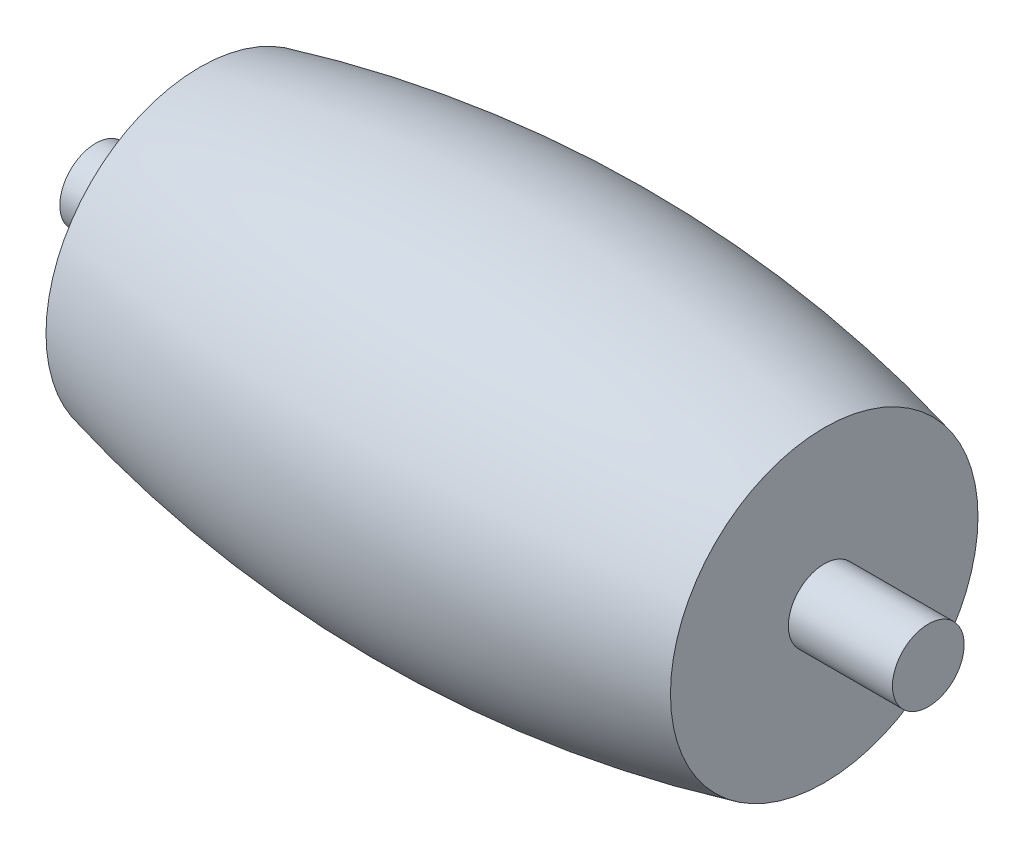
SolidWorks part; units mm, degrees
ref_plane "Front Plane" through (0, 0, 0) normal (0, 0, 1) x (1, 0, 0)
ref_plane "Top Plane" through (0, 0, 0) normal (0, 1, 0) x (1, 0, 0)
ref_plane "Right Plane" through (0, 0, 0) normal (1, 0, 0) x (0, 0, -1)
sketch "Sketch1" plane through (0, 0, 0) normal (1, 0, 0) x (0, 0, -1)
  circle A0 centre (0, 0) radius 4.15
  dimension "D1" = 8.3
sketch "Sketch2" plane through (0, 0, 0) normal (0, 0, 1) x (1, 0, 0)
  line L0 (0, -4.15) -> (0, 4.15) construction
  line L1 (6.75, 0) -> (-6.75, 0)
  line L2 (-6.75, 3.3242) -> (-6.75, 0)
  line L3 (6.75, 3.3242) -> (6.75, 0)
  line L4 (-10.4952, 0) -> (15.5987, 0) construction
  arc A0 (-6.75, 3.3242) -> (6.75, 3.3242) centre (0, -23.85) cw
  dimension "D1" = 28
  dimension "D4" = 23.85
  dimension "D2" = 0
  dimension "D3" = 0
  dimension "D5" = 0
  dimension "D6" = 0
sweep "Sweep1" add profiles "Sketch2" path "Sketch1"
sketch "Sketch3" plane through (-6.75, 0, 0) normal (-1, 0, 0) x (0, 0, 1)
  circle A0 centre (0, 0) radius 0.775
extrude "Boss-Extrude1" add sketch "Sketch3" along normal blind 2.25
mirror "Mirror1" about plane through (0, 0, 0) normal (1, 0, 0) of "Boss-Extrude1"
